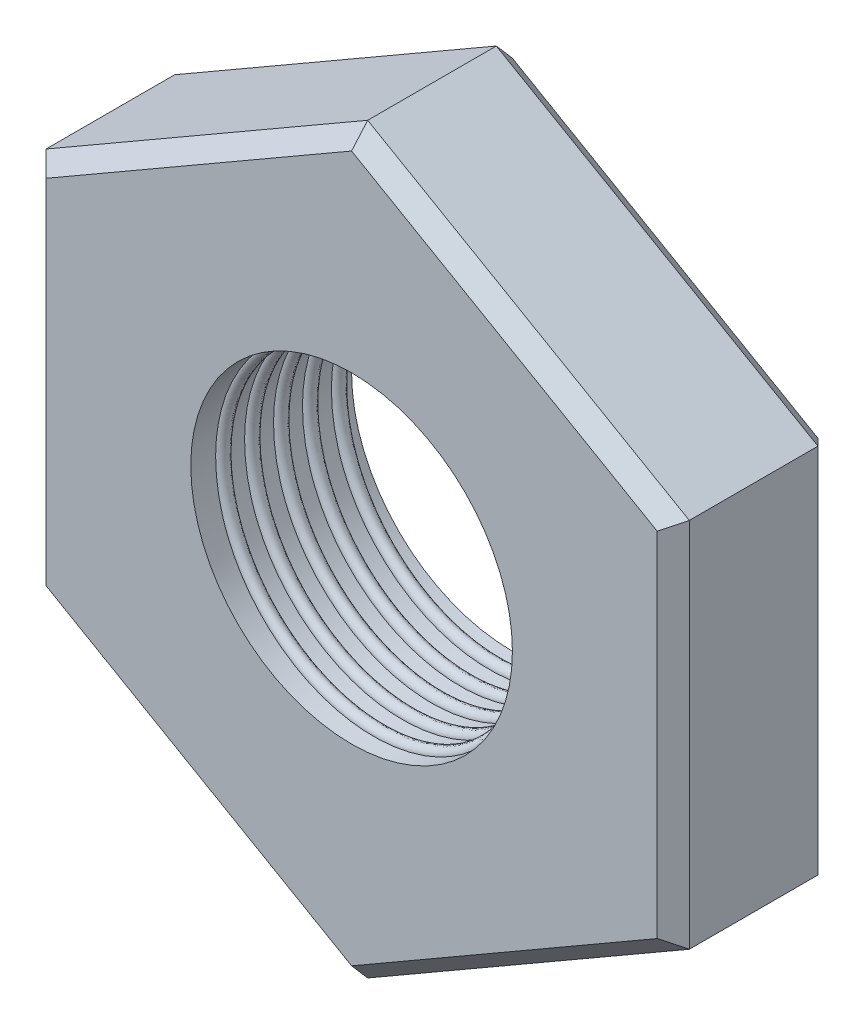
SolidWorks part; units mm, degrees
material "Cast Alloy Steel"
ref_plane "Front Plane" through (0, 0, 0) normal (0, 0, 1) x (1, 0, 0)
ref_plane "Top Plane" through (0, 0, 0) normal (0, 1, 0) x (1, 0, 0)
ref_plane "Right Plane" through (0, 0, 0) normal (1, 0, 0) x (0, 0, -1)
sketch "Sketch1" plane through (0, 0, 0) normal (0, 0, 1) x (1, 0, 0)
  line L1 (0, 11.547) -> (-10, 5.7735)
  line L2 (-10, 5.7735) -> (-10, -5.7735)
  line L3 (-10, -5.7735) -> (0, -11.547)
  line L4 (0, -11.547) -> (10, -5.7735)
  line L5 (10, -5.7735) -> (10, 5.7735)
  line L6 (10, 5.7735) -> (0, 11.547)
  circle A0 centre (0, 0) radius 10 construction
extrude "Boss-Extrude1" add sketch "Sketch1" along normal blind 5
sketch "Sketch2" plane through (0, 0, 5) normal (0, 0, 1) x (1, 0, 0)
  circle A0 centre (0, 0) radius 5
extrude "Cut-Extrude1" cut sketch "Sketch2" against normal through all both and the other way through all
sketch "Sketch3" plane through (0, 0, 5) normal (0, 0, 1) x (1, 0, 0)
  circle A0 centre (0, 0) radius 5 construction
  circle A1 centre (0, 0) radius 5
curve "Helix/Spiral1" pitch 0.9 height 4.5 turns 5
sketch "Sketch4" plane through (0, 0, 0) normal (1, 0, 0) x (0, 0, -1)
  line L0 (0, 5) -> (-0.4, 5)
  arc A0 (-0.4, 5) -> (0, 5) centre (-0.2, 5) ccw
  dimension "D1" = 0.2
sweep "Sweep1" add profiles "Sketch4" path "Helix/Spiral1"
chamfer "Chamfer1" distance 0.5 angle 45 12 edges at (5, 8.6603, 0) (10, 0, 0) (5, -8.6603, 0) (-5, -8.6603, 0) (-10, 0, 0) (-5, 8.6603, 0) (5, 8.6603, 5) (10, 0, 5) (5, -8.6603, 5) (-5, -8.6603, 5) (-10, 0, 5) (-5, 8.6603, 5)
